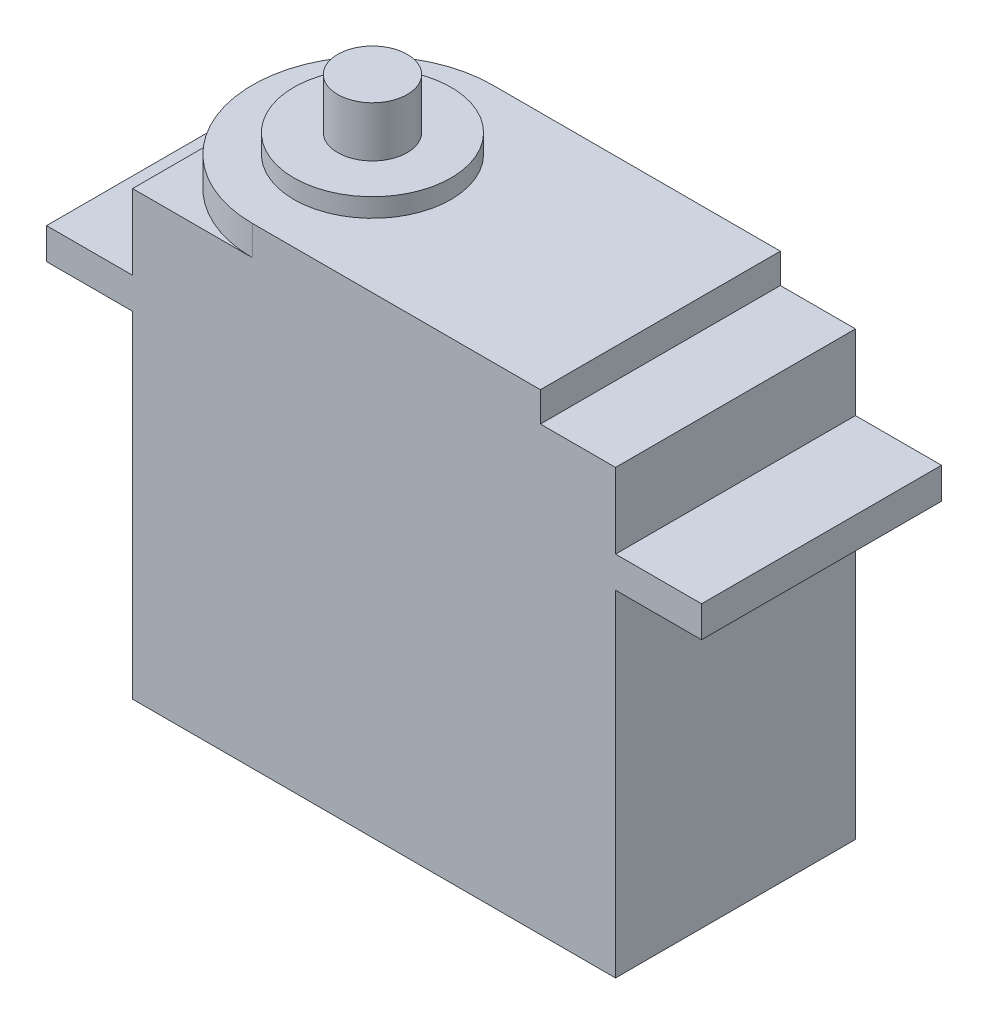
SolidWorks part; units mm, degrees
material "ABS"
ref_plane "Front Plane" through (0, 0, 0) normal (0, 0, 1) x (1, 0, 0)
ref_plane "Top Plane" through (0, 0, 0) normal (0, 1, 0) x (1, 0, 0)
ref_plane "Right Plane" through (0, 0, 0) normal (1, 0, 0) x (0, 0, -1)
sketch "Sketch1" plane through (0, 0, 0) normal (0, 1, 0) x (1, 0, 0)
  line L1 (-20.13, -10) -> (20.13, -10)
  line L2 (-20.13, -10) -> (-20.13, 10)
  line L3 (-20.13, 10) -> (20.13, 10)
  line L4 (20.13, -10) -> (20.13, 10)
  line L5 (-20.13, -10) -> (20.13, 10) construction
  line L6 (-20.13, 10) -> (20.13, -10) construction
  point P0 (0, 0)
  dimension "D1" = 20
  dimension "D2" = 40.26
extrude "Boss-Extrude1" add sketch "Sketch1" along normal blind 36.86
sketch "Sketch2" plane through (20.13, 0, 0) normal (1, 0, 0) x (0, 0, -1)
  line L0 (0, 36.86) -> (0, 0) construction
  line L1 (-10, 36.86) -> (10, 36.86) construction
  line L2 (10, 36.86) -> (10, 0) construction
  line L3 (-10, 28) -> (10, 28)
  line L4 (-10, 28) -> (-10, 30.6)
  line L5 (-10, 30.6) -> (10, 30.6)
  line L6 (10, 28) -> (10, 30.6)
  line L7 (-10, 28) -> (10, 30.6) construction
  line L8 (-10, 30.6) -> (10, 28) construction
  line L9 (-10, 0) -> (10, 0) construction
  point P5 (0, 29.3)
  dimension "D1" = 28
  dimension "D2" = 2.6
extrude "Boss-Extrude2" add sketch "Sketch2" along normal blind 7.17
sketch "Sketch3" plane through (-20.13, 0, 0) normal (-1, 0, 0) x (0, 0, 1)
  line L0 (0, 36.86) -> (0, 0) construction
  line L1 (-10, 36.86) -> (10, 36.86) construction
  line L2 (10, 36.86) -> (10, 0) construction
  line L3 (-10, 28) -> (10, 28)
  line L4 (-10, 28) -> (-10, 30.6)
  line L5 (-10, 30.6) -> (10, 30.6)
  line L6 (10, 28) -> (10, 30.6)
  line L7 (-10, 28) -> (10, 30.6) construction
  line L8 (-10, 30.6) -> (10, 28) construction
  line L9 (-10, 0) -> (10, 0) construction
  point P5 (0, 29.3)
  dimension "D1" = 2.6
  dimension "D2" = 28
extrude "Boss-Extrude3" add sketch "Sketch3" along normal blind 7.17
sketch "Sketch4" plane through (0, 36.86, 0) normal (0, 1, 0) x (1, 0, 0)
  line L0 (-20.13, 0) -> (20.13, 0) construction
  line L1 (-20.13, 10) -> (-20.13, -10) construction
  line L2 (20.13, -10) -> (20.13, 10) construction
  line L3 (0, 10) -> (0, -10) construction
  line L4 (20.13, 10) -> (-20.13, 10) construction
  line L5 (-20.13, -10) -> (20.13, -10) construction
  line L7 (-20.13, 10) -> (13.87, 10)
  line L8 (-20.13, 10) -> (-20.13, -10)
  line L9 (-20.13, -10) -> (13.87, -10)
  line L10 (13.87, 10) -> (13.87, -10)
  circle A0 centre (-10.13, 0) radius 10
  line M2 (20.13, 10) -> (-20.13, 10)
  dimension "D1" = 34
  dimension "D2" = 10
extrude "Boss-Extrude4" add sketch "Sketch4" along normal blind 2.48 contours A0 | A0 L9 L10 M2
sketch "Sketch5" plane through (0, 39.34, 0) normal (0, 1, 0) x (1, 0, 0)
  line L0 (-10.13, 10) -> (-10.13, -10) construction
  line L1 (13.87, 10) -> (-10.13, 10) construction
  arc A0 (-10.13, 10) -> (-10.13, -10) centre (-10.13, 0) ccw construction
  circle A1 centre (-10.13, 0) radius 6.55
  dimension "D1" = 13.1
extrude "Boss-Extrude5" add sketch "Sketch5" along normal blind 1.56
sketch "Sketch6" plane through (0, 40.9, 0) normal (0, 1, 0) x (1, 0, 0)
  line L0 (-10.13, 6.55) -> (-10.13, -6.55) construction
  circle A0 centre (-10.13, 0) radius 6.55 construction
  circle A1 centre (-10.13, 0) radius 6.55 construction
  circle A2 centre (-10.13, 0) radius 2.9
  dimension "D1" = 5.8
extrude "Boss-Extrude6" add sketch "Sketch6" along normal blind 4.2
